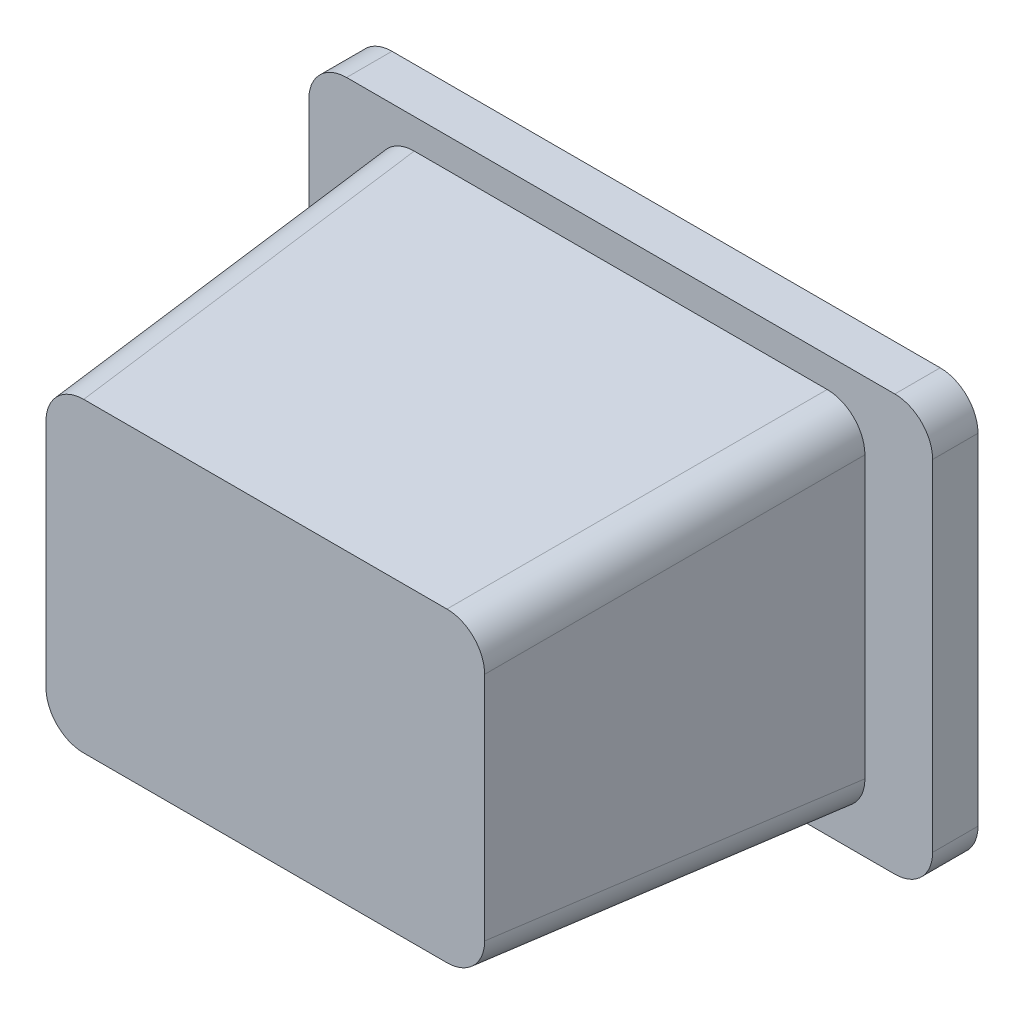
SolidWorks part; units mm, degrees
ref_plane "Front Plane" through (0, 0, 0) normal (0, 0, 1) x (1, 0, 0)
ref_plane "Top Plane" through (0, 0, 0) normal (0, 1, 0) x (1, 0, 0)
ref_plane "Right Plane" through (0, 0, 0) normal (1, 0, 0) x (0, 0, -1)
sketch "Sketch1" plane through (0, 0, 0) normal (0, 0, 1) x (1, 0, 0)
  line L1 (-91.2185, 67.1429) -> (38.7815, 67.1429)
  line L2 (-91.2185, 67.1429) -> (-91.2185, -27.8571)
  line L3 (-91.2185, -27.8571) -> (38.7815, -27.8571)
  line L4 (38.7815, 67.1429) -> (38.7815, -27.8571)
  dimension "D1" = 130
  dimension "D2" = 95
extrude "Boss-Extrude1" add sketch "Sketch1" along normal blind 100 draft 4
sketch "Sketch2" plane through (0, 0, 0) normal (0, 0, 1) x (1, 0, 0)
  line L0 (-26.2185, 67.1429) -> (-26.2185, -36.4018) construction
  line L1 (56.2815, 74.6429) -> (-108.7185, 74.6429)
  line L2 (56.2815, 74.6429) -> (56.2815, -35.3571)
  line L3 (56.2815, -35.3571) -> (-108.7185, -35.3571)
  line L4 (-108.7185, 74.6429) -> (-108.7185, -35.3571)
  line L5 (38.7815, 67.1429) -> (-91.2185, 67.1429) construction
  line L6 (38.7815, 19.6429) -> (-126.7239, 19.6429) construction
  line L7 (38.7815, -27.8571) -> (38.7815, 67.1429) construction
  point P12 (0, 0)
  point P13 (56.2815, 19.6429)
  point P14 (-26.2185, -35.3571)
  dimension "D1" = 165
  dimension "D2" = 110
  dimension "D3" = 0
  dimension "D4" = 0
extrude "Boss-Extrude2" add sketch "Sketch2" along normal mid plane 12
fillet "Fillet1" radius 10 4 edges at (35.0754, 63.4367, 53) (35.0754, -24.151, 53) (-87.5124, -24.151, 53) (-87.5124, 63.4367, 53)
fillet "Fillet2" radius 10 4 edges at (56.2815, 74.6429, 0) (56.2815, -35.3571, 0) (-108.7185, -35.3571, 0) (-108.7185, 74.6429, 0)
